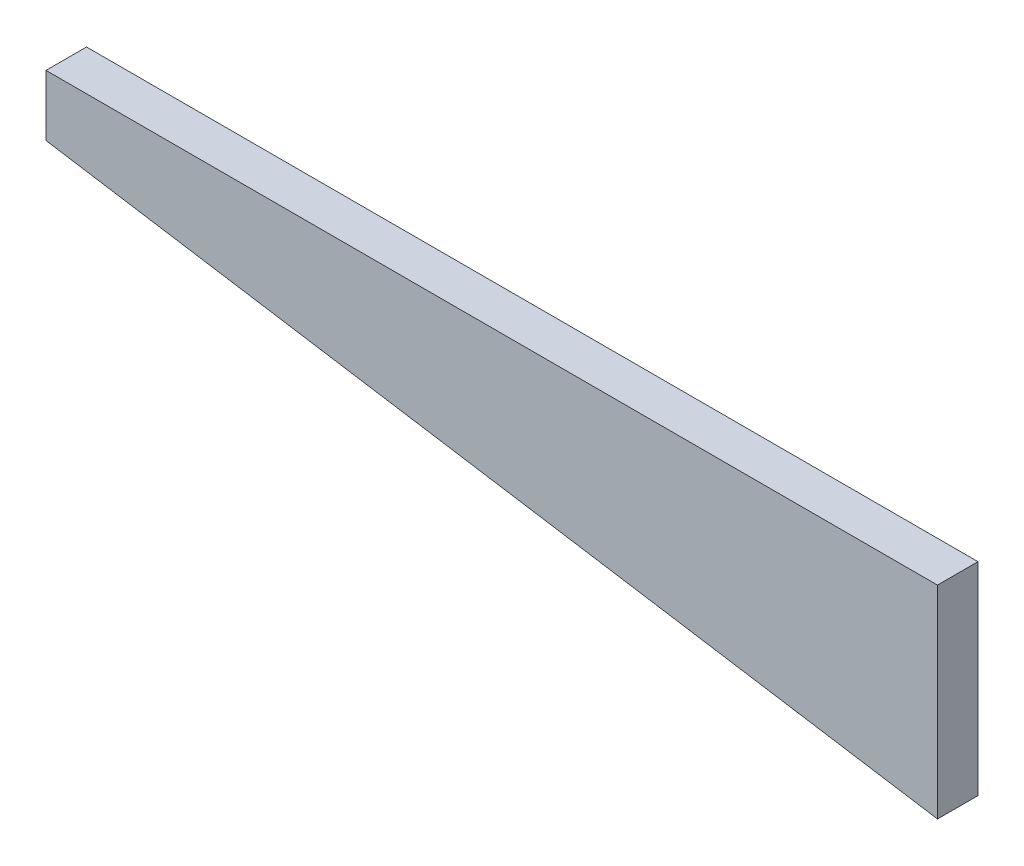
SolidWorks part; units mm, degrees
material "AISI 1045 Steel, cold drawn"
ref_plane "Front Plane" through (0, 0, 0) normal (0, 0, 1) x (1, 0, 0)
ref_plane "Top Plane" through (0, 0, 0) normal (0, 1, 0) x (1, 0, 0)
ref_plane "Right Plane" through (0, 0, 0) normal (1, 0, 0) x (0, 0, -1)
sketch "Sketch1" plane through (0, 0, 0) normal (0, 0, 1) x (1, 0, 0)
  line L0 (0, 0) -> (0, 50)
  line L1 (0, 50) -> (-220, 50)
  line L3 (-220, 50) -> (-220, 35)
  line L4 (-220, 35) -> (0, 0)
  dimension "D1" = 50
  dimension "D2" = 220
  dimension "D3" = 15
extrude "Boss-Extrude1" add sketch "Sketch1" along normal mid plane 10
